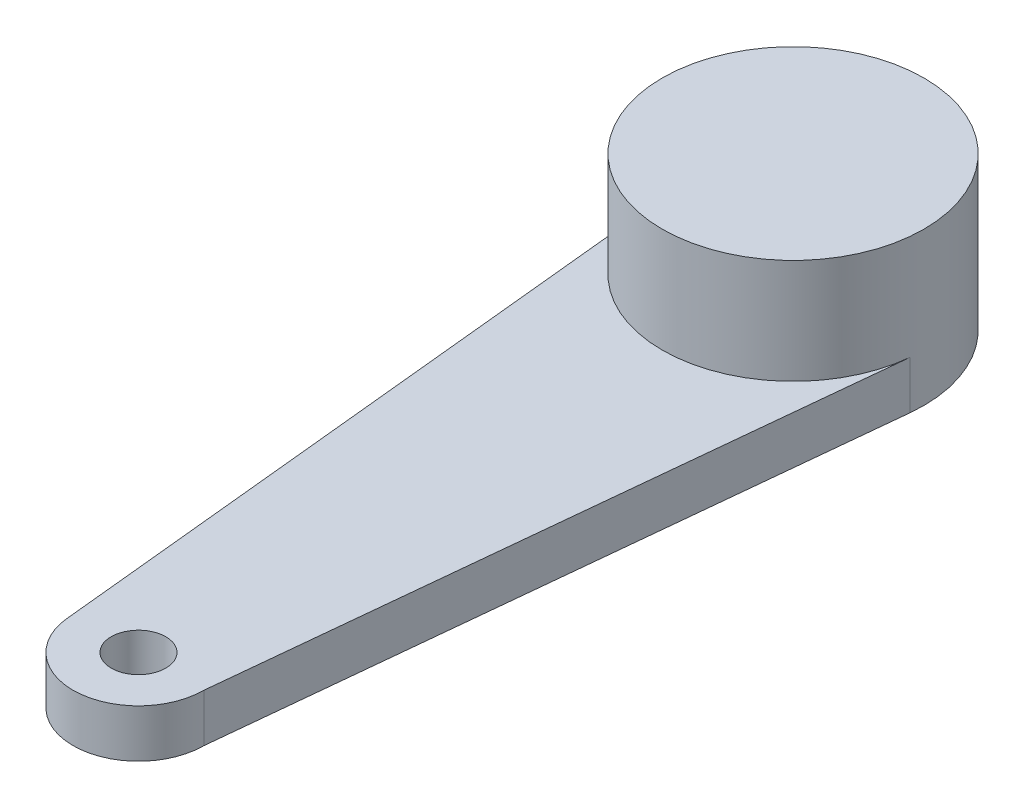
SolidWorks part; units mm, degrees
ref_plane "Front Plane" through (0, 0, 0) normal (0, 0, 1) x (1, 0, 0)
ref_plane "Top Plane" through (0, 0, 0) normal (0, 1, 0) x (1, 0, 0)
ref_plane "Right Plane" through (0, 0, 0) normal (1, 0, 0) x (0, 0, -1)
sketch "Sketch1" plane through (0, 0, 0) normal (0, 1, 0) x (1, 0, 0)
  circle A0 centre (0, 0) radius 3
  dimension "D1" = 6
extrude "Boss-Extrude1" add sketch "Sketch1" along normal blind 3.5
sketch "Sketch2" plane through (0, 0, 0) normal (0, 1, 0) x (1, 0, 0)
  line L0 (-2.985, -0.3) -> (-1.4925, -15.15)
  line L1 (2.9848, -0.3015) -> (1.5, -15)
  circle A0 centre (0, -15) radius 0.625
  circle A1 centre (0, -15) radius 1.5
  circle A2 centre (0, 0) radius 3
  circle A3 centre (0, 0) radius 3 construction
  dimension "D2" = 1.25
  dimension "D3" = 3
  dimension "D1" = 15
extrude "Boss-Extrude2" add sketch "Sketch2" along normal blind 1.1 contours A1 A0 | A2 L0 A1 L1
